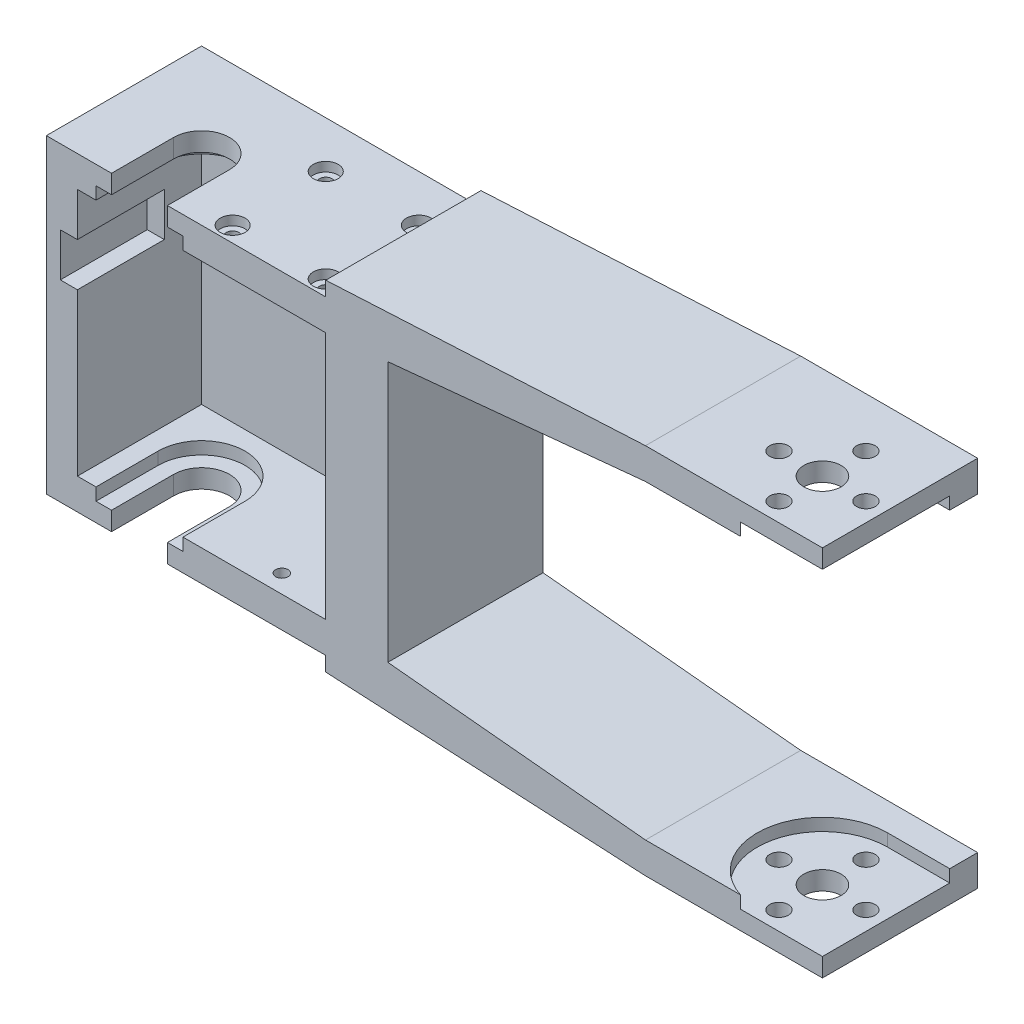
SolidWorks part; units mm, degrees
ref_plane "Alzado" through (0, 0, 0) normal (0, 0, 1) x (1, 0, 0)
ref_plane "Planta" through (0, 0, 0) normal (0, 1, 0) x (1, 0, 0)
ref_plane "Vista lateral" through (0, 0, 0) normal (1, 0, 0) x (0, 0, -1)
sketch "Croquis3" plane through (0, 0, 0) normal (0, 0, 1) x (1, 0, 0)
  line L0 (0, 0) -> (0, 40) construction
  line L1 (0, 40) -> (40, 40) construction
  line L2 (40, 40) -> (40, 0) construction
  line L3 (40, 0) -> (0, 0) construction
  line L4 (0, 40) -> (-5, 40) construction
  line L5 (-5, 40) -> (-5, 45) construction
  line L6 (-5, 45) -> (129.2112, 45) construction
  line L7 (0, 0) -> (10, 0) construction
  line L8 (10, 0) -> (10, 45) construction
  line L9 (10, 45) -> (110, 45) construction
  line L10 (110, 45) -> (110, 0) construction
  line L11 (110, 45) -> (110, 50) construction
  line L12 (110, 50) -> (91.5, 50) construction
  line L13 (91.5, 50) -> (91.5, 0) construction
  line L14 (91.5, 0) -> (110, 0) construction
  line L15 (40, 40) -> (47, 40) construction
  line L16 (91.5, 50) -> (-5, 45) construction
  line L17 (110, 50) -> (120, 50) construction
  line L18 (120, 50) -> (120, 0) construction
  line L19 (120, 0) -> (110, 0) construction
  line L20 (0, 20) -> (153.5623, 20) construction
  line L21 (120, -10) -> (120, 40) construction
  line L22 (110, -10) -> (120, -10) construction
  line L23 (91.5, -10) -> (-5, -5) construction
  line L24 (40, 0) -> (47, 0) construction
  line L25 (91.5, -10) -> (91.5, 40) construction
  line L26 (110, -10) -> (91.5, -10) construction
  line L27 (110, -5) -> (110, -10) construction
  line L28 (110, -5) -> (110, 40) construction
  line L29 (10, -5) -> (110, -5) construction
  line L30 (10, 40) -> (10, -5) construction
  line L31 (-5, -5) -> (129.2112, -5) construction
  line L32 (-5, 0) -> (-5, -5) construction
  line L33 (0, 0) -> (-5, 0) construction
  line L34 (0, 0) -> (40, 0) construction
  line L35 (-5, 45) -> (91.5, 50)
  line L36 (91.5, 50) -> (120, 50)
  line L37 (120, 50) -> (120, 45)
  line L38 (120, 45) -> (91.5, 45)
  line L39 (91.5, 45) -> (91.5, -5)
  line L40 (91.5, -5) -> (120, -5)
  line L41 (120, -5) -> (120, -10)
  line L42 (120, -10) -> (91.5, -10)
  line L43 (91.5, -10) -> (-5, -5)
  line L44 (-5, -5) -> (-5, 45)
extrude "Saliente-Extruir2" add sketch "Croquis3" along normal blind 25
sketch "Croquis4" plane through (0, 0, 25) normal (0, 0, 1) x (1, 0, 0)
  line L0 (-5, 45) -> (0, 45) construction
  line L2 (0, 0) -> (40, 0)
  line L3 (0, 0) -> (0, 40)
  line L4 (0, 40) -> (40, 40)
  line L5 (40, 0) -> (40, 40)
extrude "Cortar-Extruir1" cut sketch "Croquis4" against normal blind 20
sketch "Croquis5" plane through (0, 40, 0) normal (0, -1, 0) x (1, 0, 0)
  line L0 (0, 25) -> (0, 15) construction
  line L1 (91.5, 25) -> (-5, 25) construction
  line L2 (40, 25) -> (0, 25) construction
  line L3 (0, 15) -> (10, 15) construction
  line L4 (17, 15) -> (17, 25)
  line L5 (3, 15) -> (3, 25)
  line L6 (3, 25) -> (17, 25)
  circle A0 centre (10, 15) radius 7
  line M1 (40, 25) -> (0, 25)
extrude "Cortar-Extruir2" cut sketch "Croquis5" against normal blind 2 and the other way blind 42 contours A0 L4 L5 M1 | A0
sketch "Croquis6" plane through (0, 40, 0) normal (0, -1, 0) x (1, 0, 0)
  line L0 (14.5, 15) -> (14.5, 25)
  line L1 (17, 25) -> (3, 25) construction
  line L2 (14.5, 25) -> (5.5, 25)
  line L3 (5.5, 25) -> (5.5, 15)
  circle A0 centre (10, 15) radius 4.5
extrude "Cortar-Extruir3" cut sketch "Croquis6" against normal through all and the other way through all contours A0 | A0 L0 L2 L3
sketch "Croquis7" plane through (0, 0, 25) normal (0, 0, 1) x (1, 0, 0)
  line L0 (-5, 45) -> (120, 45) construction
  line L1 (10, 40) -> (10, 45.7772) construction
  line L2 (3, 40) -> (17, 40) construction
  line L3 (14.5, 46.0104) -> (5.5, 45.544) construction
  line L4 (40, 45) -> (40, 47.3316)
  line L5 (91.5, 50) -> (14.5, 46.0104) construction
  line L6 (40, 47.3316) -> (0.6183, 66.0229)
  line L7 (0.6183, 66.0229) -> (-9.3596, 45)
  line L8 (-9.3596, 45) -> (-5, 45)
  line L9 (-5, 45) -> (40, 45)
  line L10 (91.5, 45) -> (40, 40) construction
  line L11 (50, 40.9709) -> (50, -0.9709)
  line L12 (40, 40) -> (50, 40) construction
  line L13 (50, 40.9709) -> (91.5, 45)
  line L14 (91.5, 45) -> (107.2897, 33.7815)
  line L15 (107.2897, 33.7815) -> (107.2897, 2.272)
  line L16 (107.2897, 2.272) -> (91.5, -5)
  line L17 (91.5, -5) -> (91.5, 45) construction
  line L18 (91.5, -5) -> (40, 0) construction
  line L19 (120, -5) -> (91.5, -5) construction
  line L20 (91.5, -5) -> (50, -0.9709)
  line L21 (40, 45) -> (40, -7.3316)
  line L22 (14.5, -6.0104) -> (91.5, -10) construction
  line L23 (-5, -5) -> (40, -5)
  line L24 (40, -5) -> (40, -13.476)
  line L25 (40, -13.476) -> (-6.2203, -9.2413)
  line L26 (-6.2203, -9.2413) -> (-5, -5)
  circle A0 centre (9.9788, 45) radius 14.9788 construction
  line M1 (91.5, 50) -> (14.5, 46.0104)
  line M2 (14.5, 46.0104) -> (14.5, 42)
  line M10 (14.5, -2) -> (14.5, -6.0104)
  line M11 (14.5, -6.0104) -> (91.5, -10)
  line M15 (91.5, -5) -> (91.5, 45)
extrude "Cortar-Extruir4" cut sketch "Croquis7" against normal through all contours L20 L13 L11 M15 | L9 L4 M2 M1 | L8 L9 L6 L7 M2 M1 | L23 L21 M10 M11 | L26 L25 L24 L23 M11 M10
sketch "Croquis8" plane through (0, 0, 25) normal (0, 0, 1) x (1, 0, 0)
  line L0 (40, 40) -> (40, 33) construction
  line L1 (0, 0) -> (40, 0) construction
  line L2 (17, 0) -> (40, 0) construction
  line L3 (40, 0) -> (40, 40) construction
  line L4 (43, 33) -> (43, 26)
  line L5 (40, 33) -> (43, 33)
  line L6 (40, 33) -> (40, 26)
  line L7 (40, 26) -> (43, 26)
sketch "Croquis9" plane through (0, 50, 0) normal (0, 1, 0) x (1, 0, 0)
  line L0 (120, 0) -> (120, -25) construction
  line L1 (120, -25) -> (120, -15) construction
  line L2 (120, -15) -> (110, -15) construction
  circle A0 centre (110, -15) radius 3
  circle A1 centre (110, -15) radius 7 construction
  circle A2 centre (110, -8) radius 1.5
  circle A3 centre (117, -15) radius 1.5
  circle A4 centre (110, -15) radius 3
  circle A5 centre (110, -22) radius 1.5
  circle A6 centre (110, -15) radius 3
  circle A7 centre (103, -15) radius 1.5
  circle A8 centre (110, -15) radius 3
  point P22 (110, -15)
  dimension "D1" = 4
extrude "Cortar-Extruir6" cut sketch "Croquis9" against normal blind 61 contours A2 | A0 | A3 | A5 | A7
sketch "Croquis10" plane through (0, 45, 0) normal (0, -1, 0) x (1, 0, 0)
  line L0 (110, 25.5) -> (132.3054, 25.5)
  line L1 (132.3054, 25.5) -> (132.3054, 4.5)
  line L2 (132.3054, 4.5) -> (110, 4.5)
  circle A0 centre (110, 15) radius 10.5
  circle M1 centre (103, 15) radius 1.5
  circle M2 centre (110, 22) radius 1.5
  circle M3 centre (117, 15) radius 1.5
  circle M4 centre (110, 15) radius 3
  circle M5 centre (110, 8) radius 1.5
  line M7 (120, 0) -> (120, 25)
  line M8 (120, 25) -> (91.5, 25)
extrude "Cortar-Extruir7" cut sketch "Croquis10" against normal blind 2 and the other way blind 52 contours A0 M7 M8 M1 M3 M5 M4 M2 | A0 L2 L1 L0 M7 M8
sketch "Croquis11" plane through (0, -5, 0) normal (0, 1, 0) x (1, 0, 0)
  line L1 (110, -4.5) -> (127.9826, -4.5)
  line L2 (110, -4.5) -> (110, -27.1535)
  line L3 (110, -27.1535) -> (127.9826, -27.1535)
  line L4 (127.9826, -4.5) -> (127.9826, -27.1535)
  arc A0 (120, -11.7984) -> (106.7984, -25) centre (110, -15) ccw construction
  arc A1 (120, -11.7984) -> (106.7984, -25) centre (110, -15) ccw construction
extrude "Cortar-Extruir8" cut sketch "Croquis11" against normal blind 2 and the other way blind 52
sketch "Croquis13" plane through (0, 0, 0) normal (0, 1, 0) x (1, 0, 0)
  line L0 (10, -15) -> (40, -15) construction
  line L1 (40, 0) -> (40, -25) construction
  line L2 (40, -15) -> (40, -7.5) construction
  line L3 (40, -7.5) -> (1.2203, -7.5) construction
  line L4 (40, -15) -> (40, -22.5) construction
  line L5 (40, -22.5) -> (22.5, -22.5) construction
  line L6 (22.5, -22.5) -> (22.5, -7.5) construction
  line L7 (40, -7.5) -> (40, -5) construction
  line L8 (40, -5) -> (37.5, -5) construction
  line L9 (37.5, -5) -> (37.5, -22.5) construction
  circle A0 centre (37.5, -7.5) radius 1
  circle A1 centre (37.5, -22.5) radius 1
  circle A2 centre (22.5, -22.5) radius 1
  circle A3 centre (22.5, -7.5) radius 1
extrude "Cortar-Extruir9" cut sketch "Croquis13" along normal blind 70
sketch "Croquis14" plane through (0, 0, 0) normal (0, 1, 0) x (1, 0, 0)
  line L0 (10, -15) -> (40, -15) construction
  line L1 (40, 0) -> (40, -25) construction
  line L2 (40, -15) -> (30, -5) construction
  line L3 (40, -15) -> (40, -5) construction
  line L4 (40, 0) -> (40, -25) construction
  line L5 (40, -5) -> (30, -5) construction
  line L6 (40, -15) -> (30, -25) construction
  line L7 (17, -25) -> (40, -25) construction
  line L8 (30, -25) -> (30, -5) construction
  line L9 (37.0711, -15) -> (30, -7.9289) construction
  line L10 (37.0711, -15) -> (30, -22.0711) construction
  circle A0 centre (37.0711, -15) radius 1
  circle A1 centre (30, -7.9289) radius 1
  circle A2 centre (30, -22.0711) radius 1
extrude "Cortar-Extruir10" cut sketch "Croquis14" against normal blind 70
sketch "Croquis15" plane through (0, 45, 0) normal (0, 1, 0) x (1, 0, 0)
  circle A0 centre (22.5, -7.5) radius 2
  circle A1 centre (37.5, -7.5) radius 2
  circle A2 centre (37.5, -22.5) radius 2
  circle A3 centre (22.5, -22.5) radius 2
extrude "Cortar-Extruir11" cut sketch "Croquis15" against normal blind 1.5
sketch "Croquis16" plane through (0, -5, 0) normal (0, -1, 0) x (1, 0, 0)
  circle A0 centre (30, 22.0711) radius 2
  circle A1 centre (37.0711, 15) radius 2
  circle A2 centre (30, 7.9289) radius 2
extrude "Cortar-Extruir12" cut sketch "Croquis16" against normal blind 1.5
sketch "Croquis18" plane through (0, 0, 25) normal (0, 0, 1) x (1, 0, 0)
  line L0 (43, 33) -> (-2.75, 33) construction
  line L1 (43, 26) -> (-2.75, 26) construction
  line L2 (-2.75, 33) -> (-2.75, 26) construction
  line L3 (-2.75, 33) -> (-2.75, 45) construction
  line L4 (-5, 45) -> (5.5, 45) construction
  line L5 (-2.75, 45) -> (0, 40) construction
  line L6 (0, 40) -> (0.25, 45) construction
  line L7 (0.25, 45) -> (-2.75, 45) construction
  line L8 (0, 40) -> (0, 0) construction
  line L9 (-2.75, 33) -> (0, 33)
  line L10 (-2.75, 33) -> (-2.75, 26)
  line L11 (-2.75, 26) -> (0, 26)
  line L12 (0, 33) -> (0, 26)
extrude "Cortar-Extruir13" cut sketch "Croquis18" against normal blind 14
